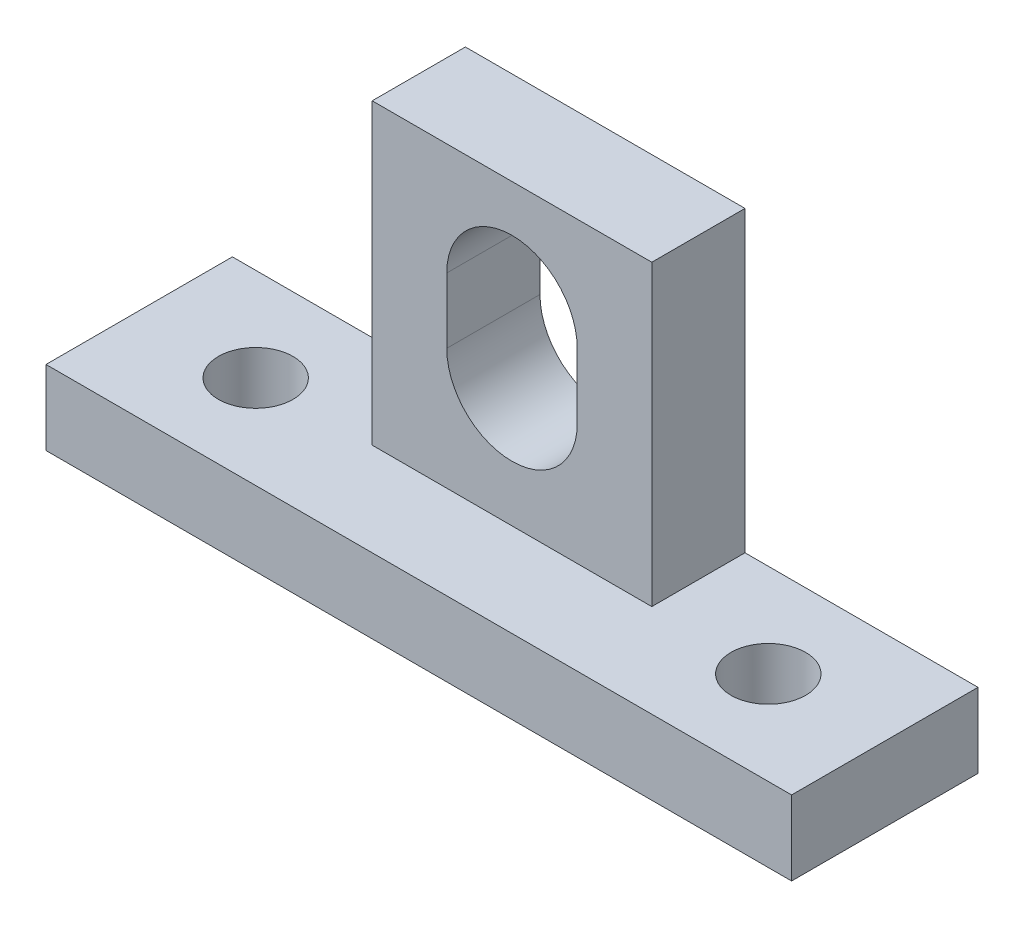
SolidWorks part; units mm, degrees
ref_plane "Plano frontal" through (0, 0, 0) normal (0, 0, 1) x (1, 0, 0)
ref_plane "Plano superior" through (0, 0, 0) normal (0, 1, 0) x (1, 0, 0)
ref_plane "Plano direito" through (0, 0, 0) normal (1, 0, 0) x (0, 0, -1)
sketch "Esboço4" plane through (0, 0, 0) normal (0, 0, 1) x (1, 0, 0)
  line L0 (-7.5, 20) -> (-7.5, 4)
  line L1 (-7.5, 20) -> (7.5, 20)
  line L2 (-20, 4) -> (-20, 0)
  line L3 (-20, 0) -> (20, 0)
  line L4 (20, 4) -> (20, 0)
  line L5 (3.5, 14) -> (3.5, 10.5)
  line L7 (-7.5, 4) -> (-20, 4)
  line L8 (0, 20) -> (0, 0) construction
  line L9 (7.5, 4) -> (20, 4)
  line L10 (7.5, 20) -> (7.5, 4)
  line L11 (-3.5, 10.5) -> (-3.5, 14)
  arc A0 (3.5, 14) -> (-3.5, 14) centre (0, 14) ccw
  arc A1 (-3.5, 10.5) -> (3.5, 10.5) centre (0, 10.5) ccw
  point P0 (0, 0)
  dimension "D1" = 7
  dimension "D2" = 3.5
  dimension "D3" = 14
  dimension "D5" = 15
  dimension "D6" = 4
  dimension "D7" = 40
  dimension "D8" = 20
extrude "Ressalto-extrusão2" add sketch "Esboço4" along normal blind 10
sketch "Esboço5" plane through (0, 4, 0) normal (0, 1, 0) x (1, 0, 0)
  line L0 (-20, 0) -> (-7.5, -10) construction
  line L1 (0, 0) -> (0, -10) construction
  line L2 (7.5, -10) -> (-7.5, -10) construction
  circle A0 centre (-13.75, -5) radius 2
  circle A1 centre (13.75, -5) radius 2
  dimension "D1" = 4
extrude "Corte-extrusão3" cut sketch "Esboço5" against normal blind 15
sketch "Esboço6" plane through (-7.5, 0, 0) normal (-1, 0, 0) x (0, 0, 1)
  line L0 (5, 20) -> (5, 4)
  line L1 (10, 20) -> (0, 20) construction
  line L2 (10, 4) -> (0, 4) construction
  line L3 (5, 4) -> (10, 4)
  line L4 (10, 4) -> (10, 20)
  line L5 (10, 20) -> (5, 20)
  line L6 (0, 20) -> (0, 4) construction
  dimension "D1" = 5
extrude "Corte-extrusão4" cut sketch "Esboço6" against normal blind 15
